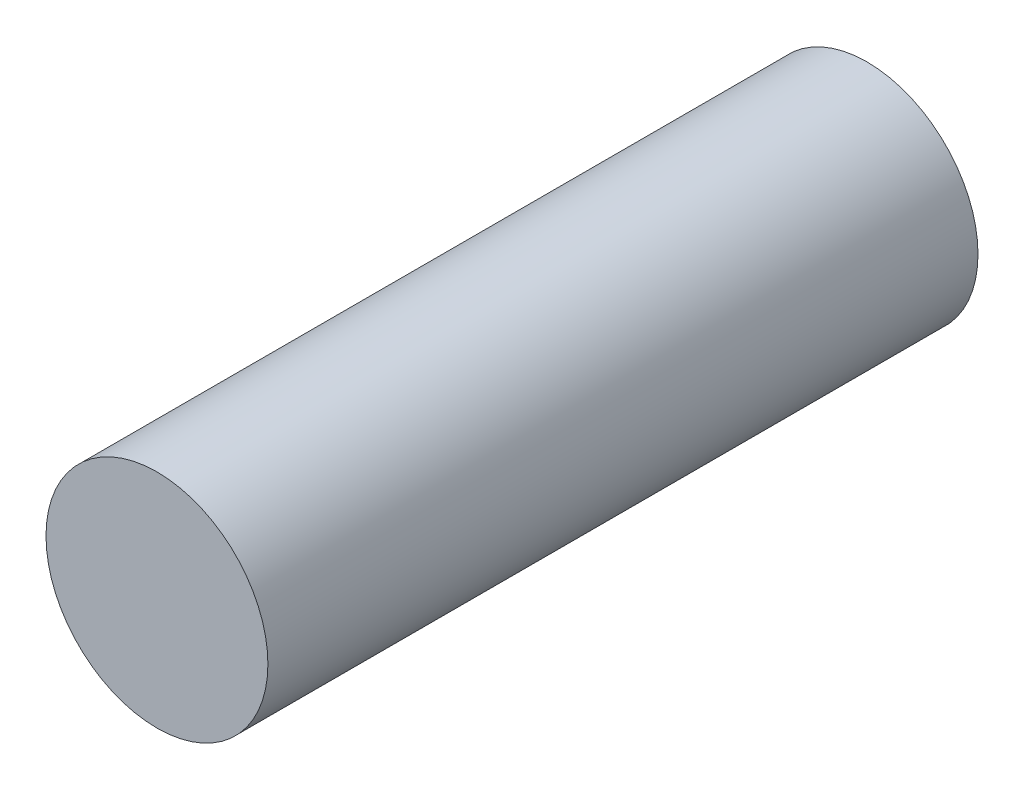
SolidWorks part; units mm, degrees
ref_plane "정면" through (0, 0, 0) normal (0, 0, 1) x (1, 0, 0)
ref_plane "윗면" through (0, 0, 0) normal (0, 1, 0) x (1, 0, 0)
ref_plane "우측면" through (0, 0, 0) normal (1, 0, 0) x (0, 0, -1)
sketch "스케치1" plane through (0, 0, 0) normal (0, 0, 1) x (1, 0, 0)
  circle A0 centre (0, 0) radius 5
  dimension "D1" = 10
extrude "보스-돌출1" add sketch "스케치1" along normal blind 32
